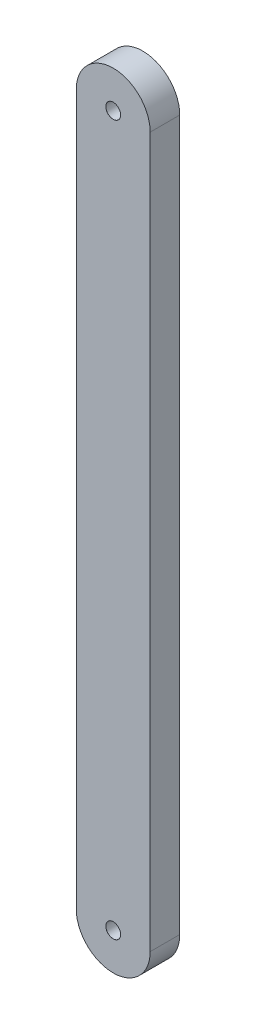
SolidWorks part; units mm, degrees
material "Alloy Steel"
ref_plane "Front Plane" through (0, 0, 0) normal (0, 0, 1) x (1, 0, 0)
ref_plane "Top Plane" through (0, 0, 0) normal (0, 1, 0) x (1, 0, 0)
ref_plane "Right Plane" through (0, 0, 0) normal (1, 0, 0) x (0, 0, -1)
sketch "Sketch1" plane through (0, 0, 0) normal (0, 0, 1) x (1, 0, 0)
  line L0 (0, 0) -> (0, 480)
  line L1 (50, 480) -> (50, 0)
  arc A0 (0, 480) -> (50, 480) centre (25, 480) cw
  arc A1 (50, 0) -> (0, 0) centre (25, 0) cw
  point P7 (0, 240)
  dimension "D1" = 480
  dimension "D2" = 50
extrude "Boss-Extrude1" add sketch "Sketch1" along normal blind 20
hole_wizard "Ø10.0mm Dowel Hole1" positions "Sketch2" profile "Sketch3" hole size "Ø10.0" standard "ANSI Metric" end condition up to next
sketch "Sketch2" plane through (0, 0, 20) normal (0, 0, 1) x (1, 0, 0)
  point P0 (25, 480)
  point P3 (25, 0)
sketch "Sketch3" plane through (25, 480, 20) normal (1, 0, 0) x (0, -1, 0)
  line L0 (0, 0) -> (0, 20)
  line L1 (0, 20) -> (5, 20)
  line L2 (5, 20) -> (5, 0.025)
  line L3 (5, 0.025) -> (5.025, 0)
  line L5 (5.025, 0) -> (0, 0)
  line L6 (-5, 0.025) -> (-5.025, 0) construction
  line L11 (0, -6.35) -> (0, 107.95) construction
  dimension "Thru Hole Dia." = 10
  dimension "Thru Hole Depth" = 20
  dimension "Near C'Sink Dia." = 10.05
  dimension "Near C'Sink Angle" = 90
scale "Scale1" scale about centroid uniform scaling yes scale factor 0.125
